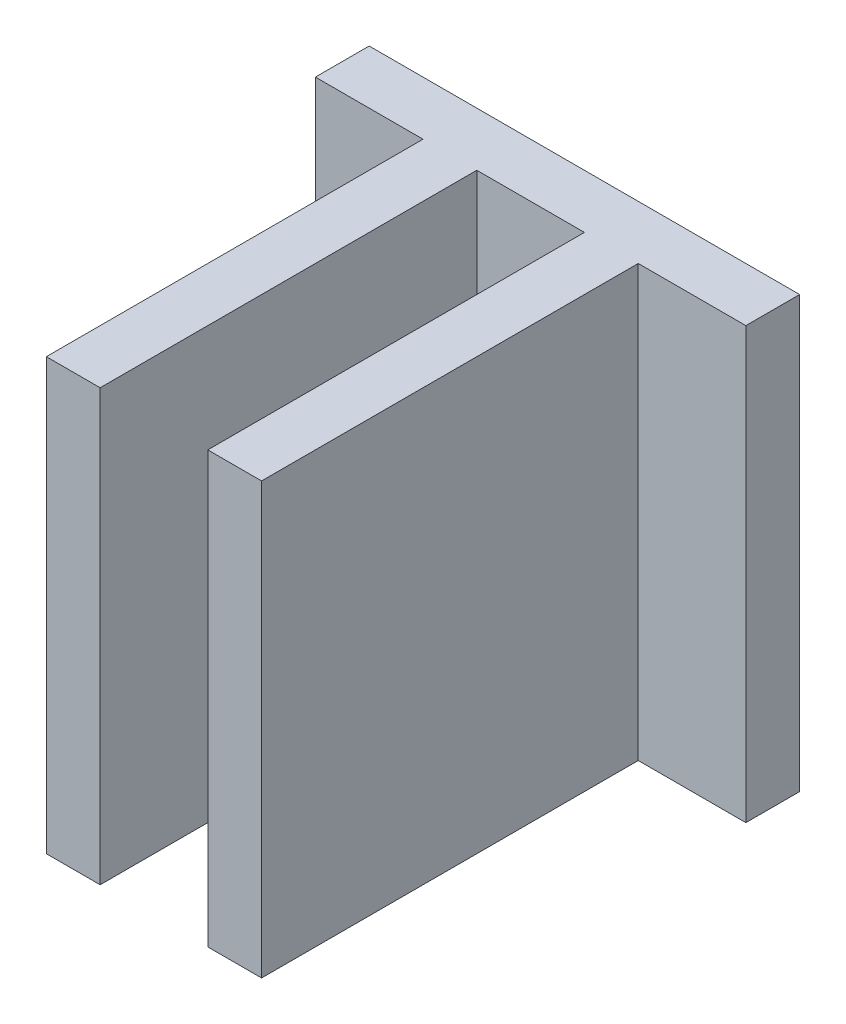
SolidWorks part; units mm, degrees
ref_plane "Front Plane" through (0, 0, 0) normal (0, 0, 1) x (1, 0, 0)
ref_plane "Top Plane" through (0, 0, 0) normal (0, 1, 0) x (1, 0, 0)
ref_plane "Right Plane" through (0, 0, 0) normal (1, 0, 0) x (0, 0, -1)
sketch "Sketch1" plane through (0, 0, 0) normal (0, 1, 0) x (1, 0, 0)
  line L0 (0, 0) -> (25.4, 0)
  line L1 (25.4, 0) -> (25.4, -3.175)
  line L2 (25.4, -3.175) -> (19.05, -3.175)
  line L3 (19.05, -3.175) -> (19.05, -25.4)
  line L4 (19.05, -25.4) -> (15.875, -25.4)
  line L5 (15.875, -25.4) -> (15.875, -3.175)
  line L6 (15.875, -3.175) -> (9.525, -3.175)
  line L7 (9.525, -3.175) -> (9.525, -25.4)
  line L8 (9.525, -25.4) -> (6.35, -25.4)
  line L9 (6.35, -25.4) -> (6.35, -3.175)
  line L10 (6.35, -3.175) -> (0, -3.175)
  line L11 (0, -3.175) -> (0, 0)
  point P12 (0, 0)
  point P14 (12.7, -3.175)
  point P15 (12.7, 0)
  point P16 (0, 0)
  dimension "D1" = 3.175
  dimension "D2" = 25.4
  dimension "D3" = 6.35
  dimension "D4" = 25.4
extrude "Boss-Extrude1" add sketch "Sketch1" along normal blind 25.4
